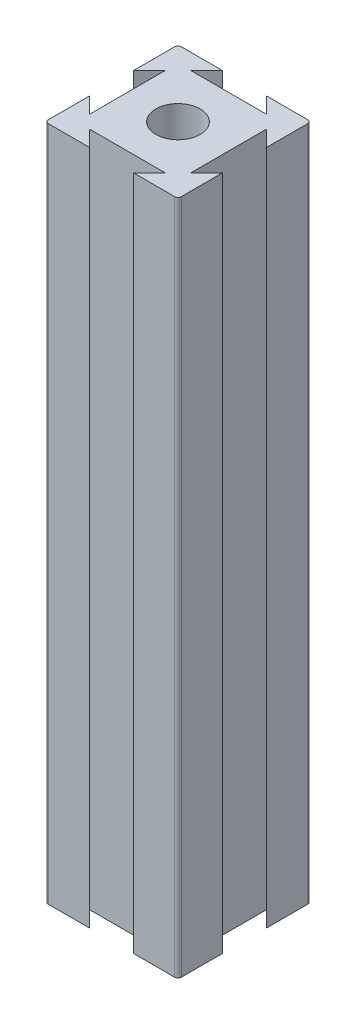
SolidWorks part; units mm, degrees
material "Alumina"
ref_plane "Front Plane" through (0, 0, 0) normal (0, 0, 1) x (1, 0, 0)
ref_plane "Top Plane" through (0, 0, 0) normal (0, 1, 0) x (1, 0, 0)
ref_plane "Right Plane" through (0, 0, 0) normal (1, 0, 0) x (0, 0, -1)
sketch "Sketch1" plane through (0, 0, 0) normal (0, 1, 0) x (1, 0, 0)
  line L0 (6.6667, 20) -> (4.285, 17.6183)
  line L1 (0, 0) -> (20, 0)
  line L2 (0, 0) -> (0, 20)
  line L3 (0, 20) -> (20, 20)
  line L4 (20, 0) -> (20, 20)
  line L5 (4.285, 17.6183) -> (15.715, 17.6183)
  line L6 (15.715, 17.6183) -> (13.3333, 20)
  line L7 (13.3333, 20) -> (6.6667, 20)
  line L8 (0, 10) -> (20, 10) construction
  line L9 (10, 20) -> (10, 0) construction
  line L10 (15.715, 2.3817) -> (13.3333, 0)
  line L11 (4.285, 2.3817) -> (15.715, 2.3817)
  line L12 (6.6667, 0) -> (4.285, 2.3817)
  line L13 (13.3333, 0) -> (6.6667, 0)
  line L14 (0, 13.3333) -> (2.3817, 15.715)
  line L15 (2.3817, 15.715) -> (2.3817, 4.285)
  line L16 (2.3817, 4.285) -> (0, 6.6667)
  line L17 (0, 6.6667) -> (0, 13.3333)
  line L18 (17.6183, 4.285) -> (20, 6.6667)
  line L19 (17.6183, 15.715) -> (17.6183, 4.285)
  line L20 (20, 13.3333) -> (17.6183, 15.715)
  line L21 (20, 6.6667) -> (20, 13.3333)
  circle A0 centre (10, 10) radius 3.3333
  dimension "D1" = 20
  dimension "D2" = 20
  dimension "D3" = 6.6667
  dimension "D4" = 6.6667
  dimension "D5" = 45
  dimension "D6" = 45
  dimension "D7" = 11.43
  dimension "D8" = 6.6667
  dimension "D9" = 6.6667
  dimension "D10" = 11.43
  dimension "D11" = 45
  dimension "D12" = 45
extrude "Boss-Extrude1" add sketch "Sketch1" along normal blind 101.6 contours L20 L4 L3 L6 L5 L0 L2 L14 L15 L16 L1 L12 L11 L10 L18 L19 A0
fillet "Fillet4" radius 0.508 4 edges at (0, 50.8, -20) (20, 50.8, -20) (0, 50.8, 0) (20, 50.8, 0)
